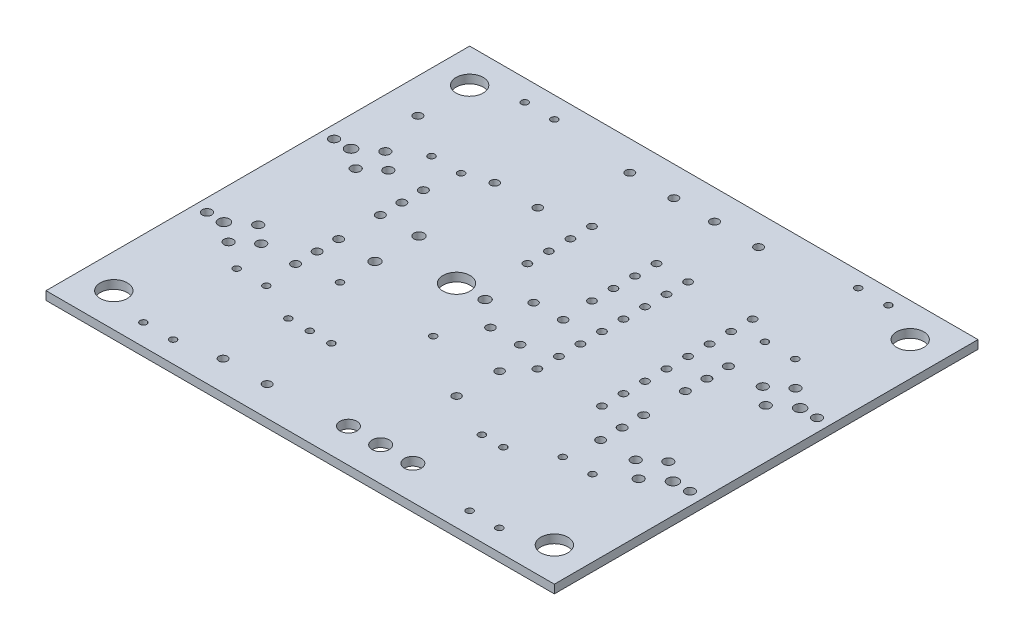
SolidWorks part; units mm, degrees
ref_plane "Plan de face" through (0, 0, 0) normal (0, 0, 1) x (1, 0, 0)
ref_plane "Plan de dessus" through (0, 0, 0) normal (0, 1, 0) x (1, 0, 0)
ref_plane "Plan de droite" through (0, 0, 0) normal (1, 0, 0) x (0, 0, -1)
sketch "Esquisse2" plane through (0, 0, 0) normal (0, 1, 0) x (1, 0, 0)
  line L1 (0, 0) -> (60, 0)
  line L2 (0, 0) -> (0, 50)
  line L3 (0, 50) -> (60, 50)
  line L4 (60, 0) -> (60, 50)
  circle A0 centre (16.4262, 27.5996) radius 0.5994
  circle A1 centre (16.4262, 22.4003) radius 0.5994
  circle A2 centre (26.8249, 25.0012) radius 0.5994
  circle A3 centre (23.4696, 24.9809) radius 1.6002
  circle A4 centre (22.6009, 3.5001) radius 0.5004
  circle A5 centre (17.399, 3.5001) radius 0.5004
  circle A6 centre (29.9999, 27.5412) radius 0.4826
  circle A7 centre (29.9999, 22.4612) radius 0.4826
  circle A8 centre (33.5001, 27.5412) radius 0.4826
  circle A9 centre (33.5001, 22.4612) radius 0.4826
  circle A10 centre (15.461, 37.5006) radius 0.4826
  circle A11 centre (20.541, 37.5006) radius 0.4826
  circle A12 centre (35.0012, 13.4595) radius 0.4826
  circle A13 centre (35.0012, 18.5395) radius 0.4826
  circle A14 centre (42.9946, 10.9906) radius 0.3988
  circle A15 centre (40.4546, 10.9906) radius 0.3988
  circle A16 centre (1.4986, 32.5018) radius 0.5512
  circle A17 centre (7.8994, 32.5018) radius 0.5512
  circle A18 centre (5.7988, 30.7518) radius 0.5512
  circle A19 centre (5.7988, 34.2519) radius 0.5512
  circle A20 centre (3.5001, 32.5018) radius 0.6502
  circle A21 centre (1.4986, 17.5006) radius 0.5512
  circle A22 centre (7.8994, 17.5006) radius 0.5512
  circle A23 centre (5.7988, 15.7505) radius 0.5512
  circle A24 centre (5.7988, 19.2507) radius 0.5512
  circle A25 centre (3.5001, 17.5006) radius 0.6502
  circle A26 centre (58.5013, 32.4993) radius 0.5512
  circle A27 centre (52.1005, 32.4993) radius 0.5512
  circle A28 centre (54.2011, 34.2494) radius 0.5512
  circle A29 centre (54.2011, 30.7492) radius 0.5512
  circle A30 centre (56.4998, 32.4993) radius 0.6502
  circle A31 centre (58.5013, 17.4981) radius 0.5512
  circle A32 centre (52.1005, 17.4981) radius 0.5512
  circle A33 centre (54.2011, 19.2481) radius 0.5512
  circle A34 centre (54.2011, 15.748) radius 0.5512
  circle A35 centre (56.4998, 17.4981) radius 0.6502
  circle A36 centre (4.0005, 45.9994) radius 1.6002
  circle A37 centre (55.9994, 45.9994) radius 1.6002
  circle A38 centre (55.9994, 4.0005) radius 1.6002
  circle A39 centre (4.0005, 4.0005) radius 1.6002
  circle A41 centre (25.6489, 38.7883) radius 0.4496
  circle A42 centre (25.6489, 36.2483) radius 0.4496
  circle A43 centre (25.6489, 33.7083) radius 0.4496
  circle A44 centre (25.6489, 31.1683) radius 0.4496
  circle A45 centre (33.2689, 31.1683) radius 0.4496
  circle A46 centre (33.2689, 33.7083) radius 0.4496
  circle A47 centre (33.2689, 36.2483) radius 0.4496
  circle A48 centre (33.2689, 38.7883) radius 0.4496
  circle A49 centre (36.9926, 38.7858) radius 0.4496
  circle A50 centre (36.9926, 36.2458) radius 0.4496
  circle A51 centre (36.9926, 33.7058) radius 0.4496
  circle A52 centre (36.9926, 31.1658) radius 0.4496
  circle A53 centre (36.9926, 28.6258) radius 0.4496
  circle A54 centre (36.9926, 26.0858) radius 0.4496
  circle A55 centre (36.9926, 23.5458) radius 0.4496
  circle A56 centre (36.9926, 21.0058) radius 0.4496
  circle A57 centre (44.6126, 21.0058) radius 0.4496
  circle A58 centre (44.6126, 23.5458) radius 0.4496
  circle A59 centre (44.6126, 26.0858) radius 0.4496
  circle A60 centre (44.6126, 28.6258) radius 0.4496
  circle A61 centre (44.6126, 31.1658) radius 0.4496
  circle A62 centre (44.6126, 33.7058) radius 0.4496
  circle A63 centre (44.6126, 36.2458) radius 0.4496
  circle A64 centre (44.6126, 38.7858) radius 0.4496
  circle A65 centre (17.145, 11.4605) radius 0.3988
  circle A66 centre (19.685, 11.4605) radius 0.3988
  circle A67 centre (22.225, 11.4605) radius 0.3988
  circle A68 centre (22.4003, 46.4998) radius 0.5004
  circle A69 centre (27.5996, 46.4998) radius 0.5004
  circle A70 centre (32.4002, 46.4998) radius 0.5004
  circle A71 centre (37.5996, 46.4998) radius 0.5004
  circle A72 centre (8.9992, 36.4998) radius 0.3988
  circle A73 centre (8.9992, 47.5005) radius 0.3988
  circle A74 centre (12.4993, 13.5001) radius 0.3988
  circle A75 centre (12.4993, 2.4994) radius 0.3988
  circle A76 centre (8.9992, 13.5001) radius 0.3988
  circle A77 centre (8.9992, 2.4994) radius 0.3988
  circle A78 centre (47.5005, 2.4994) radius 0.3988
  circle A79 centre (47.5005, 13.5001) radius 0.3988
  circle A80 centre (51.0007, 13.5001) radius 0.3988
  circle A81 centre (51.0007, 2.4994) radius 0.3988
  circle A82 centre (12.4993, 36.4998) radius 0.3988
  circle A83 centre (12.4993, 47.5005) radius 0.3988
  circle A84 centre (47.6631, 37.1907) radius 0.3988
  circle A85 centre (47.6631, 48.1914) radius 0.3988
  circle A86 centre (51.2013, 37.2262) radius 0.3988
  circle A87 centre (51.2013, 48.227) radius 0.3988
  circle A88 centre (16.4998, 18.1991) radius 0.3988
  circle A89 centre (27.5006, 18.1991) radius 0.3988
  circle A90 centre (35.499, 4.0005) radius 1.0008
  circle A91 centre (39.2989, 4.0005) radius 1.0008
  circle A92 centre (31.6992, 4.0005) radius 1.0008
  circle A93 centre (11.999, 27.4599) radius 0.5004
  circle A94 centre (11.999, 29.9999) radius 0.5004
  circle A95 centre (11.999, 32.5399) radius 0.5004
  circle A96 centre (11.999, 17.46) radius 0.5004
  circle A97 centre (11.999, 20) radius 0.5004
  circle A98 centre (11.999, 22.54) radius 0.5004
  circle A99 centre (48.0009, 27.4599) radius 0.5004
  circle A100 centre (48.0009, 29.9999) radius 0.5004
  circle A101 centre (48.0009, 32.5399) radius 0.5004
  circle A102 centre (48.0009, 17.46) radius 0.5004
  circle A103 centre (48.0009, 20) radius 0.5004
  circle A104 centre (48.0009, 22.54) radius 0.5004
  circle A105 centre (4.0767, 39.8196) radius 0.5004
extrude "Extrusion1" add sketch "Esquisse2" along normal blind 1
